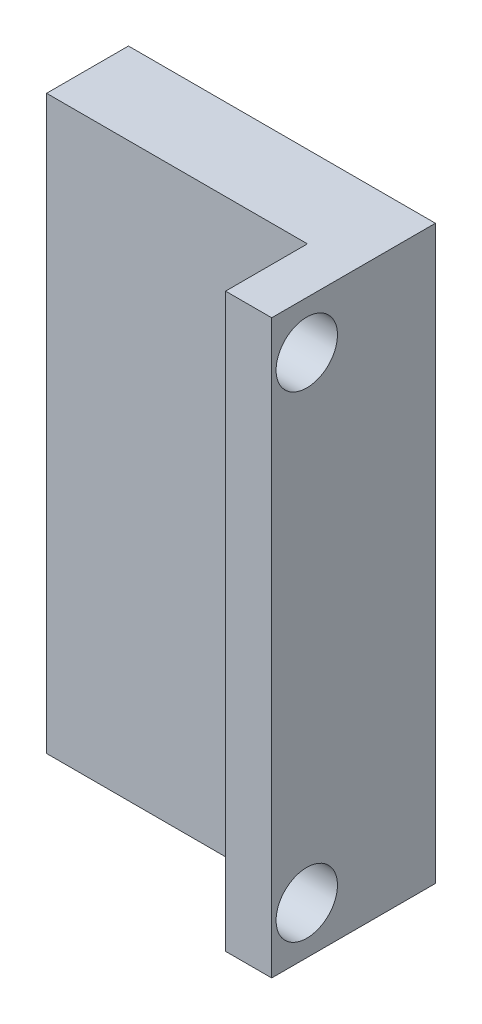
SolidWorks part; units mm, degrees
ref_plane "Front Plane" through (0, 0, 0) normal (0, 0, 1) x (1, 0, 0)
ref_plane "Top Plane" through (0, 0, 0) normal (0, 1, 0) x (1, 0, 0)
ref_plane "Right Plane" through (0, 0, 0) normal (1, 0, 0) x (0, 0, -1)
sketch "Sketch2" plane through (0, 0, 0) normal (0, 0, 1) x (1, 0, 0)
  line L1 (0, 0) -> (10, 0)
  line L2 (0, 0) -> (0, 10)
  line L3 (0, 10) -> (10, 10)
  line L4 (10, 0) -> (10, 10)
  dimension "D1" = 10
  dimension "D2" = 10
extrude "Boss-Extrude1" add sketch "Sketch2" along normal blind 5
sketch "Sketch4" plane through (0, 0, 5) normal (0, 0, 1) x (1, 0, 0)
  line L0 (0, 18.97) -> (0, -8.97)
  line L1 (0, -8.97) -> (15, -8.97)
  line L2 (15, -8.97) -> (15, 18.97)
  line L3 (15, 18.97) -> (0, 18.97)
  line L4 (0, 0) -> (10, 0) construction
  line L7 (10, 0) -> (10, 10) construction
  dimension "D1" = 270
  dimension "D2" = 27.94
  dimension "D3" = 10
  dimension "D4" = 8.97
  dimension "D5" = 15
extrude "Boss-Extrude4" add sketch "Sketch4" along normal blind 4
sketch "Sketch5" plane through (0, 0, 9) normal (0, 0, 1) x (1, 0, 0)
  line L0 (0, -8.97) -> (15, -8.97) construction
  line L1 (15, 18.97) -> (12.7455, 18.97)
  line L2 (15, 18.97) -> (15, -8.97)
  line L3 (15, -8.97) -> (12.7455, -8.97)
  line L4 (12.7455, 18.97) -> (12.7455, -8.97)
extrude "Boss-Extrude5" add sketch "Sketch5" along normal blind 4
sketch "Sketch6" plane through (12.7455, 0, 0) normal (-1, 0, 0) x (0, 0, 1)
  line L0 (9, 18.97) -> (9, -8.97) construction
  line L2 (13, -8.97) -> (9, -8.97) construction
  circle A0 centre (11.286, 16.6443) radius 1.5
  circle A1 centre (11.286, -6.645) radius 1.5
  dimension "D1" = 3
  dimension "D2" = 3
  dimension "D3" = 2.286
  dimension "D4" = 2.286
  dimension "D5" = 23.2893
  dimension "D6" = 2.325
extrude "Cut-Extrude1" cut sketch "Sketch6" against normal blind 40
sketch "Sketch7" plane through (0, 0, 0) normal (0, 0, -1) x (-1, 0, 0)
  line L0 (0, 10) -> (0, 0) construction
  line L1 (-10, 10) -> (0, 10) construction
  circle A0 centre (-5, 5) radius 3.5
  dimension "D1" = 7
  dimension "D2" = 5
  dimension "D3" = 5
extrude "Boss-Extrude6" add sketch "Sketch7" along normal blind 8
sketch "Sketch8" plane through (0, 0, -8) normal (0, 0, -1) x (-1, 0, 0)
  line L1 (0, 10) -> (-10, 10)
  line L2 (0, 10) -> (0, 0)
  line L3 (0, 0) -> (-10, 0)
  line L4 (-10, 10) -> (-10, 0)
extrude "Cut-Extrude2" cut sketch "Sketch8" against normal up to surface (13 mm away) up to face at (6.25, 5, 5)
